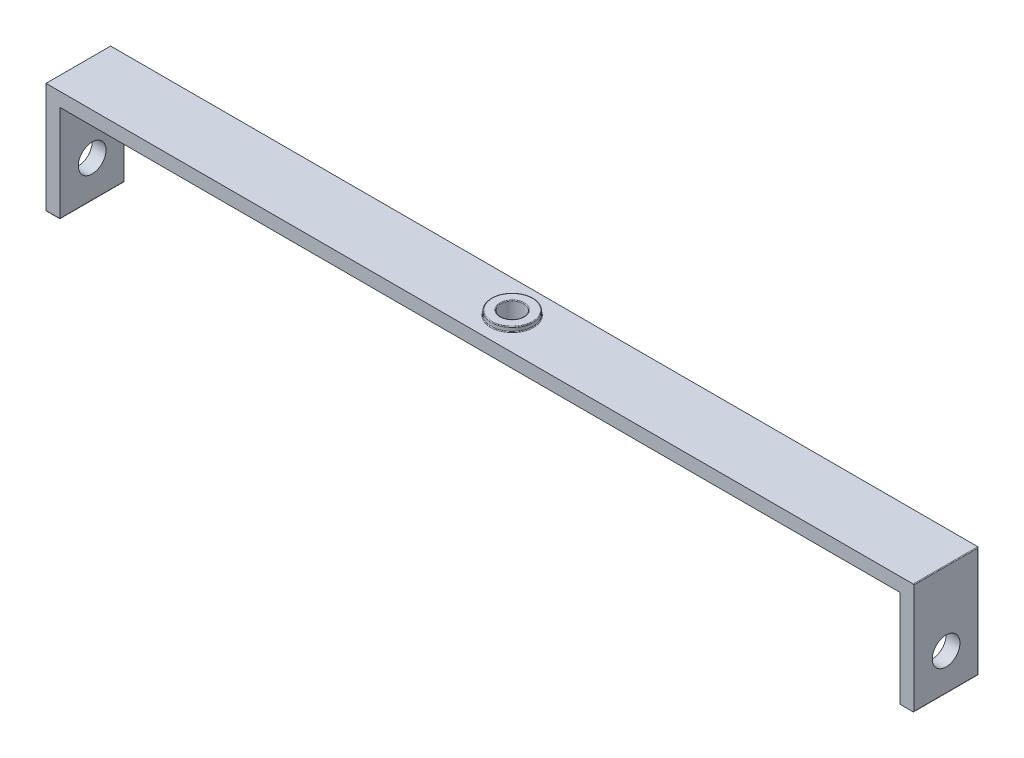
SolidWorks part; units mm, degrees
ref_plane "Front Plane" through (0, 0, 0) normal (0, 0, 1) x (1, 0, 0)
ref_plane "Top Plane" through (0, 0, 0) normal (0, 1, 0) x (1, 0, 0)
ref_plane "Right Plane" through (0, 0, 0) normal (1, 0, 0) x (0, 0, -1)
sketch "Sketch1" plane through (0, 0, 0) normal (0, 0, 1) x (1, 0, 0)
  line L0 (-47, 0) -> (47, 0)
  line L1 (47, 0) -> (47, -12)
  line L2 (-47, 0) -> (-47, -12)
  line L3 (45.5, -1.5) -> (45.5, -12)
  line L4 (-45.5, -1.5) -> (45.5, -1.5)
  line L5 (-45.5, -1.5) -> (-45.5, -12)
  line L6 (-47, -12) -> (-45.5, -12)
  line L7 (45.5, -12) -> (47, -12)
  point P4 (0, 0)
  dimension "D1" = 94
  dimension "D2" = 12
  dimension "D3" = 1.5
extrude "Boss-Extrude1" add sketch "Sketch1" along normal mid plane 7
sketch "Sketch2" plane through (0, 0, 0) normal (0, 1, 0) x (1, 0, 0)
  circle A0 centre (0, 0) radius 1.25
  dimension "D1" = 2.5
extrude "Cut-Extrude1" cut sketch "Sketch2" against normal through all
sketch "Sketch3" plane through (0, 0, 0) normal (0, 1, 0) x (1, 0, 0)
  circle A0 centre (0, 0) radius 1.25 construction
  circle A1 centre (0, 0) radius 1.25
  circle A2 centre (0, 0) radius 2.25
  dimension "D1" = 1
extrude "Boss-Extrude2" add sketch "Sketch3" along normal blind 0.5
sketch "Sketch4" plane through (0, 0, 0) normal (1, 0, 0) x (0, 0, -1)
  line L0 (0, 0) -> (0, -8) construction
  line L1 (1.25, 0.5) -> (-1.25, 0.5) construction
  circle A0 centre (0, -8) radius 1.5
  dimension "D1" = 8.5
  dimension "D2" = 3
extrude "Cut-Extrude2" cut sketch "Sketch4" against normal through all both and the other way through all
fillet "Fillet1" radius 0.075 18 edges at (-45.5, -6.75, -3.5) (0, -1.5, -3.5) (0, 0, -2.25) (47, -12, 0) (47, 0, 0) (-47, -12, 0) (-45.5, -12, 0) (-45.5, -1.5, 0) (45.5, -1.5, 0) (45.5, -12, 0) (-46.25, -12, 3.5) (45.5, -6.75, -3.5) (-46.25, -12, -3.5) (47, -6, -3.5) (46.25, -12, -3.5) (0, -1.5, 1.25) (0, 0.5, 2.25) (0, 0.5, 1.25)
